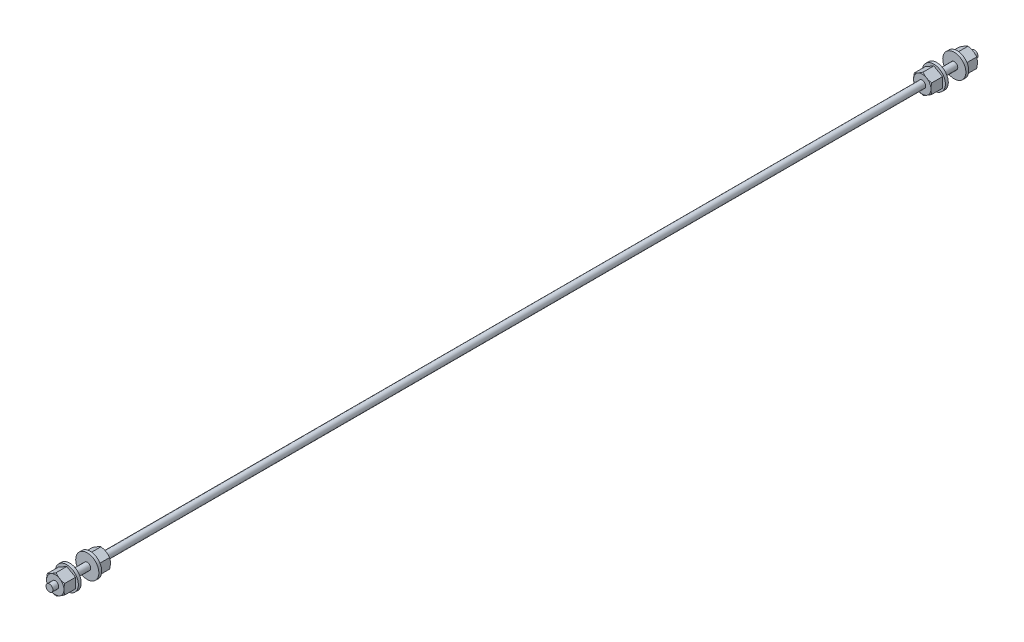
SolidWorks part; units mm, degrees
material "AISI 304"
ref_plane "Front Plane" through (0, 0, 0) normal (0, 0, 1) x (1, 0, 0)
ref_plane "Top Plane" through (0, 0, 0) normal (0, 1, 0) x (1, 0, 0)
ref_plane "Right Plane" through (0, 0, 0) normal (1, 0, 0) x (0, 0, -1)
sketch "Sketch1" plane through (0, 0, 0) normal (0, 0, 1) x (1, 0, 0)
  line L1 (0, 5.4993) -> (-4.7625, 2.7496)
  line L2 (-4.7625, 2.7496) -> (-4.7625, -2.7496)
  line L3 (-4.7625, -2.7496) -> (0, -5.4993)
  line L4 (0, -5.4993) -> (4.7625, -2.7496)
  line L5 (4.7625, -2.7496) -> (4.7625, 2.7496)
  line L6 (4.7625, 2.7496) -> (0, 5.4993)
  circle A0 centre (0, 0) radius 4.7625 construction
  dimension "Hex" = 9.525
extrude "Extrude1" add sketch "Sketch1" against normal blind 7.9375
sketch "Sketch13" plane through (0, 0, -7.9375) normal (0, 0, -1) x (-1, 0, 0)
  circle A0 centre (0, 0) radius 6.35
  dimension "Flange od" = 12.7
extrude "Extrude3" add sketch "Sketch13" against normal blind 1.5875
sketch "Sketch2" plane through (0, 0, 0) normal (0, 0, 1) x (1, 0, 0)
  circle A0 centre (0, 0) radius 4.7625 construction
  circle A1 centre (0, 0) radius 4.7625
extrude "Cut-Extrude1" cut sketch "Sketch2" against normal through all draft 60 flip side to cut
sketch "Sketch4" plane through (0, 0, 0) normal (0, 0, 1) x (1, 0, 0)
  circle A0 centre (0, 0) radius 1.905
  dimension "Thread Dia" = 3.81
sketch "Sketch14" plane through (0, 0, -7.9375) normal (0, 0, -1) x (-1, 0, 0)
  circle A0 centre (0, 0) radius 1.905
  dimension "D1" = 3.81
extrude "Boss-Extrude1" add sketch "Sketch14" along normal blind 4.826
ref_plane "Plane1" through (0, 0, -12.7635) normal (0, 0, -1) x (-1, 0, 0)
mirror "Mirror1" about plane through (0, 0, -12.7635) normal (0, 0, -1) of "Extrude3", "Cut-Extrude1", "Extrude1", "Boss-Extrude1"
sketch "Sketch15" plane through (0, 0, -25.527) normal (0, 0, -1) x (-1, 0, 0)
  circle A0 centre (0, 0) radius 1.905
  dimension "D1" = 3.81
extrude "Boss-Extrude2" add sketch "Sketch15" along normal blind 225.298
ref_plane "Plane2" through (0, 0, -250.825) normal (0, 0, -1) x (-1, 0, 0)
mirror "Mirror2" about plane through (0, 0, -250.825) normal (0, 0, -1) of "Extrude3", "Cut-Extrude1", "Extrude1", "Boss-Extrude1", "Mirror1", "Boss-Extrude2"
sketch "Sketch16" plane through (0, 0, -501.65) normal (0, 0, -1) x (-1, 0, 0)
  circle A0 centre (0, 0) radius 1.905
  dimension "D1" = 3.81
extrude "Boss-Extrude3" add sketch "Sketch16" along normal blind 3.175
extrude "Boss-Extrude4" add sketch "Sketch4" along normal blind 3.175
